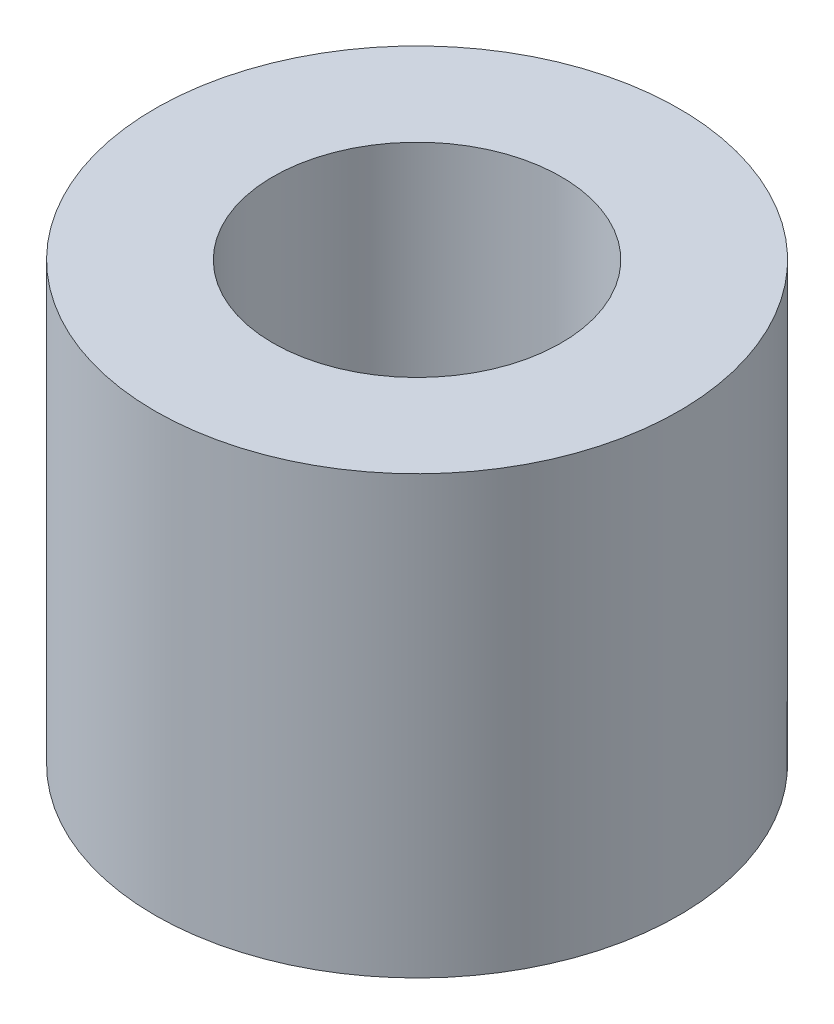
SolidWorks part; units mm, degrees
ref_plane "Front Plane" through (0, 0, 0) normal (0, 0, 1) x (1, 0, 0)
ref_plane "Top Plane" through (0, 0, 0) normal (0, 1, 0) x (1, 0, 0)
ref_plane "Right Plane" through (0, 0, 0) normal (1, 0, 0) x (0, 0, -1)
sketch "Sketch1" plane through (0, 0, 0) normal (0, 1, 0) x (1, 0, 0)
  circle A0 centre (0, 0) radius 1.65
  circle A1 centre (0, 0) radius 3
  dimension "D1" = 6
  dimension "D2" = 3.3
extrude "Boss-Extrude1" add sketch "Sketch1" along normal blind 5
